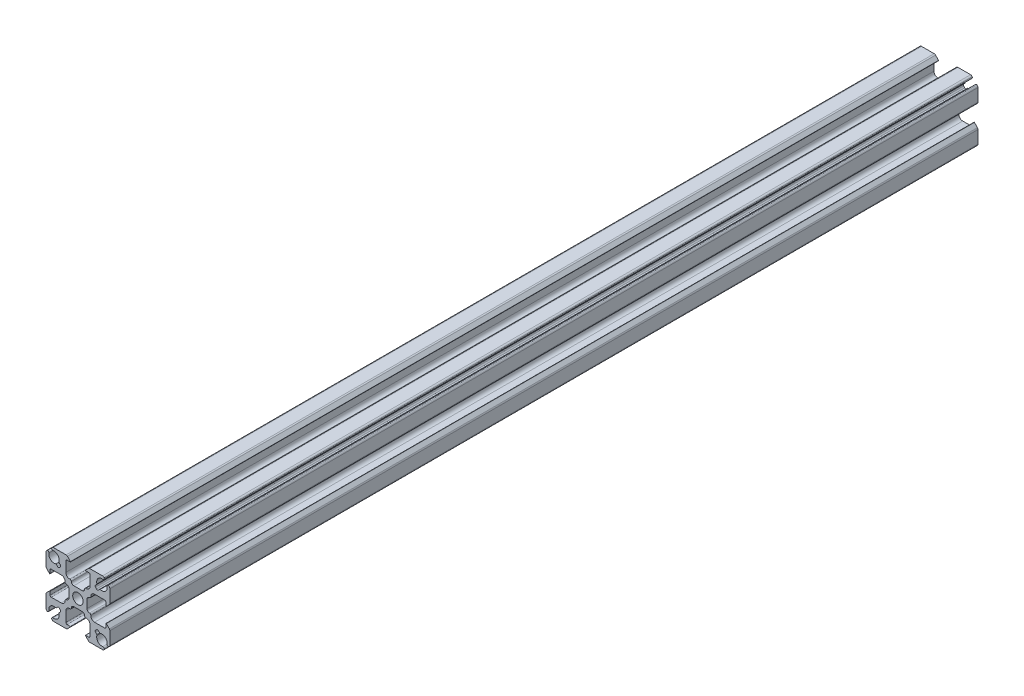
SolidWorks part; units mm, degrees
ref_plane "Front Plane" through (0, 0, 0) normal (0, 0, 1) x (1, 0, 0)
ref_plane "Top Plane" through (0, 0, 0) normal (0, 1, 0) x (1, 0, 0)
ref_plane "Right Plane" through (0, 0, 0) normal (1, 0, 0) x (0, 0, -1)
ref_plane "Plane1" through (0, 0, 0) normal (0, 0, -1) x (-1, 0, 0)
sketch "Sketch1" plane through (0, 0, 0) normal (0, 0, -1) x (-1, 0, 0)
  line L0 (-7.4885, 8.6199) -> (-6.9856, 8.117)
  line L1 (-6.9856, 7.4099) -> (-7.4099, 6.9856)
  line L2 (-8.117, 6.9856) -> (-8.6199, 7.4885)
  line L3 (-12.7, 9.7594) -> (-12.7, 4.7107)
  line L4 (-12.4803, 4.1803) -> (-11.2707, 2.9707)
  line L5 (-11.1, 3.0414) -> (-11.1, 4.325)
  line L6 (-10.6, 4.825) -> (-6.6, 4.825)
  line L7 (-5.1, 3.325) -> (-5.1, 3.15)
  line L8 (-3.6, 1.65) -> (-3.6, -1.65)
  line L9 (-5.1, -3.15) -> (-5.1, -3.325)
  line L10 (-6.6, -4.825) -> (-10.6, -4.825)
  line L11 (-11.1, -4.325) -> (-11.1, -3.0414)
  line L12 (-11.2707, -2.9707) -> (-12.4803, -4.1803)
  line L13 (-12.7, -4.7107) -> (-12.7, -9.7594)
  line L14 (-8.6199, -7.4885) -> (-8.117, -6.9856)
  line L15 (-7.4099, -6.9856) -> (-6.9856, -7.4099)
  line L16 (-6.9856, -8.117) -> (-7.4885, -8.6199)
  line L17 (-9.7594, -12.7) -> (-4.7107, -12.7)
  line L18 (-4.1803, -12.4803) -> (-2.9707, -11.2707)
  line L19 (-3.0414, -11.1) -> (-4.325, -11.1)
  line L20 (-4.825, -10.6) -> (-4.825, -6.6)
  line L21 (-3.325, -5.1) -> (-3.15, -5.1)
  line L22 (-1.65, -3.6) -> (1.65, -3.6)
  line L23 (3.15, -5.1) -> (3.325, -5.1)
  line L24 (4.825, -6.6) -> (4.825, -10.6)
  line L25 (4.325, -11.1) -> (3.0414, -11.1)
  line L26 (2.9707, -11.2707) -> (4.1803, -12.4803)
  line L27 (4.7107, -12.7) -> (9.7594, -12.7)
  line L28 (7.4885, -8.6199) -> (6.9856, -8.117)
  line L29 (6.9856, -7.4099) -> (7.4099, -6.9856)
  line L30 (8.117, -6.9856) -> (8.6199, -7.4885)
  line L31 (12.7, -9.7594) -> (12.7, -4.7107)
  line L32 (12.4803, -4.1803) -> (11.2707, -2.9707)
  line L33 (11.1, -3.0414) -> (11.1, -4.325)
  line L34 (10.6, -4.825) -> (6.6, -4.825)
  line L35 (5.1, -3.325) -> (5.1, -3.15)
  line L36 (3.6, -1.65) -> (3.6, 1.65)
  line L37 (5.1, 3.15) -> (5.1, 3.325)
  line L38 (6.6, 4.825) -> (10.6, 4.825)
  line L39 (11.1, 4.325) -> (11.1, 3.0414)
  line L40 (11.2707, 2.9707) -> (12.4803, 4.1803)
  line L41 (12.7, 4.7107) -> (12.7, 9.7594)
  line L42 (8.6199, 7.4885) -> (8.117, 6.9856)
  line L43 (7.4099, 6.9856) -> (6.9856, 7.4099)
  line L44 (6.9856, 8.117) -> (7.4885, 8.6199)
  line L45 (9.7594, 12.7) -> (4.7107, 12.7)
  line L46 (4.1803, 12.4803) -> (2.9707, 11.2707)
  line L47 (3.0414, 11.1) -> (4.325, 11.1)
  line L48 (4.825, 10.6) -> (4.825, 6.6)
  line L49 (3.325, 5.1) -> (3.15, 5.1)
  line L50 (1.65, 3.6) -> (-1.65, 3.6)
  line L51 (-3.15, 5.1) -> (-3.325, 5.1)
  line L52 (-4.825, 6.6) -> (-4.825, 10.6)
  line L53 (-4.325, 11.1) -> (-3.0414, 11.1)
  line L54 (-2.9707, 11.2707) -> (-4.1803, 12.4803)
  line L55 (-4.7107, 12.7) -> (-9.7594, 12.7)
  circle A0 centre (0, 0) radius 2.08
  arc A1 (-9.7594, 12.7) -> (-10.4266, 12.2927) centre (-9.7594, 11.95) ccw
  arc A2 (-10.4266, 12.2927) -> (-9.8933, 11.5721) centre (-9.9818, 12.0642) ccw
  arc A3 (-9.8933, 11.5721) -> (-7.5492, 8.8748) centre (-9.525, 9.525) cw
  arc A4 (-7.5492, 8.8748) -> (-7.4885, 8.6199) centre (-7.3118, 8.7967) ccw
  arc A5 (-6.9856, 8.117) -> (-6.9856, 7.4099) centre (-7.3392, 7.7635) cw
  arc A6 (-7.4099, 6.9856) -> (-8.117, 6.9856) centre (-7.7635, 7.3392) cw
  arc A7 (-8.6199, 7.4885) -> (-8.8748, 7.5492) centre (-8.7967, 7.3118) ccw
  arc A8 (-8.8748, 7.5492) -> (-11.5721, 9.8933) centre (-9.525, 9.525) cw
  arc A9 (-11.5721, 9.8933) -> (-12.2927, 10.4266) centre (-12.0642, 9.9818) ccw
  arc A10 (-12.2927, 10.4266) -> (-12.7, 9.7594) centre (-11.95, 9.7594) ccw
  arc A11 (-12.7, 4.7107) -> (-12.4803, 4.1803) centre (-11.95, 4.7107) ccw
  arc A12 (-11.2707, 2.9707) -> (-11.1, 3.0414) centre (-11.2, 3.0414) ccw
  arc A13 (-11.1, 4.325) -> (-10.6, 4.825) centre (-10.6, 4.325) cw
  arc A14 (-6.6, 4.825) -> (-5.1, 3.325) centre (-6.6, 3.325) cw
  arc A15 (-5.1, 3.15) -> (-4.6, 2.65) centre (-4.6, 3.15) ccw
  arc A16 (-4.6, 2.65) -> (-3.6, 1.65) centre (-4.6, 1.65) cw
  arc A17 (-3.6, -1.65) -> (-4.6, -2.65) centre (-4.6, -1.65) cw
  arc A18 (-4.6, -2.65) -> (-5.1, -3.15) centre (-4.6, -3.15) ccw
  arc A19 (-5.1, -3.325) -> (-6.6, -4.825) centre (-6.6, -3.325) cw
  arc A20 (-10.6, -4.825) -> (-11.1, -4.325) centre (-10.6, -4.325) cw
  arc A21 (-11.1, -3.0414) -> (-11.2707, -2.9707) centre (-11.2, -3.0414) ccw
  arc A22 (-12.4803, -4.1803) -> (-12.7, -4.7107) centre (-11.95, -4.7107) ccw
  arc A23 (-12.7, -9.7594) -> (-12.2927, -10.4266) centre (-11.95, -9.7594) ccw
  arc A24 (-12.2927, -10.4266) -> (-11.5721, -9.8933) centre (-12.0642, -9.9818) ccw
  arc A25 (-11.5721, -9.8933) -> (-8.8748, -7.5492) centre (-9.525, -9.525) cw
  arc A26 (-8.8748, -7.5492) -> (-8.6199, -7.4885) centre (-8.7967, -7.3118) ccw
  arc A27 (-8.117, -6.9856) -> (-7.4099, -6.9856) centre (-7.7635, -7.3392) cw
  arc A28 (-6.9856, -7.4099) -> (-6.9856, -8.117) centre (-7.3392, -7.7635) cw
  arc A29 (-7.4885, -8.6199) -> (-7.5492, -8.8748) centre (-7.3118, -8.7967) ccw
  arc A30 (-7.5492, -8.8748) -> (-9.8933, -11.5721) centre (-9.525, -9.525) cw
  arc A31 (-9.8933, -11.5721) -> (-10.4266, -12.2927) centre (-9.9818, -12.0642) ccw
  arc A32 (-10.4266, -12.2927) -> (-9.7594, -12.7) centre (-9.7594, -11.95) ccw
  arc A33 (-4.7107, -12.7) -> (-4.1803, -12.4803) centre (-4.7107, -11.95) ccw
  arc A34 (-2.9707, -11.2707) -> (-3.0414, -11.1) centre (-3.0414, -11.2) ccw
  arc A35 (-4.325, -11.1) -> (-4.825, -10.6) centre (-4.325, -10.6) cw
  arc A36 (-4.825, -6.6) -> (-3.325, -5.1) centre (-3.325, -6.6) cw
  arc A37 (-3.15, -5.1) -> (-2.65, -4.6) centre (-3.15, -4.6) ccw
  arc A38 (-2.65, -4.6) -> (-1.65, -3.6) centre (-1.65, -4.6) cw
  arc A39 (1.65, -3.6) -> (2.65, -4.6) centre (1.65, -4.6) cw
  arc A40 (2.65, -4.6) -> (3.15, -5.1) centre (3.15, -4.6) ccw
  arc A41 (3.325, -5.1) -> (4.825, -6.6) centre (3.325, -6.6) cw
  arc A42 (4.825, -10.6) -> (4.325, -11.1) centre (4.325, -10.6) cw
  arc A43 (3.0414, -11.1) -> (2.9707, -11.2707) centre (3.0414, -11.2) ccw
  arc A44 (4.1803, -12.4803) -> (4.7107, -12.7) centre (4.7107, -11.95) ccw
  arc A45 (9.7594, -12.7) -> (10.4266, -12.2927) centre (9.7594, -11.95) ccw
  arc A46 (10.4266, -12.2927) -> (9.8933, -11.5721) centre (9.9818, -12.0642) ccw
  arc A47 (9.8933, -11.5721) -> (7.5492, -8.8748) centre (9.525, -9.525) cw
  arc A48 (7.5492, -8.8748) -> (7.4885, -8.6199) centre (7.3118, -8.7967) ccw
  arc A49 (6.9856, -8.117) -> (6.9856, -7.4099) centre (7.3392, -7.7635) cw
  arc A50 (7.4099, -6.9856) -> (8.117, -6.9856) centre (7.7635, -7.3392) cw
  arc A51 (8.6199, -7.4885) -> (8.8748, -7.5492) centre (8.7967, -7.3118) ccw
  arc A52 (8.8748, -7.5492) -> (11.5721, -9.8933) centre (9.525, -9.525) cw
  arc A53 (11.5721, -9.8933) -> (12.2927, -10.4266) centre (12.0642, -9.9818) ccw
  arc A54 (12.2927, -10.4266) -> (12.7, -9.7594) centre (11.95, -9.7594) ccw
  arc A55 (12.7, -4.7107) -> (12.4803, -4.1803) centre (11.95, -4.7107) ccw
  arc A56 (11.2707, -2.9707) -> (11.1, -3.0414) centre (11.2, -3.0414) ccw
  arc A57 (11.1, -4.325) -> (10.6, -4.825) centre (10.6, -4.325) cw
  arc A58 (6.6, -4.825) -> (5.1, -3.325) centre (6.6, -3.325) cw
  arc A59 (5.1, -3.15) -> (4.6, -2.65) centre (4.6, -3.15) ccw
  arc A60 (4.6, -2.65) -> (3.6, -1.65) centre (4.6, -1.65) cw
  arc A61 (3.6, 1.65) -> (4.6, 2.65) centre (4.6, 1.65) cw
  arc A62 (4.6, 2.65) -> (5.1, 3.15) centre (4.6, 3.15) ccw
  arc A63 (5.1, 3.325) -> (6.6, 4.825) centre (6.6, 3.325) cw
  arc A64 (10.6, 4.825) -> (11.1, 4.325) centre (10.6, 4.325) cw
  arc A65 (11.1, 3.0414) -> (11.2707, 2.9707) centre (11.2, 3.0414) ccw
  arc A66 (12.4803, 4.1803) -> (12.7, 4.7107) centre (11.95, 4.7107) ccw
  arc A67 (12.7, 9.7594) -> (12.2927, 10.4266) centre (11.95, 9.7594) ccw
  arc A68 (12.2927, 10.4266) -> (11.5721, 9.8933) centre (12.0642, 9.9818) ccw
  arc A69 (11.5721, 9.8933) -> (8.8748, 7.5492) centre (9.525, 9.525) cw
  arc A70 (8.8748, 7.5492) -> (8.6199, 7.4885) centre (8.7967, 7.3118) ccw
  arc A71 (8.117, 6.9856) -> (7.4099, 6.9856) centre (7.7635, 7.3392) cw
  arc A72 (6.9856, 7.4099) -> (6.9856, 8.117) centre (7.3392, 7.7635) cw
  arc A73 (7.4885, 8.6199) -> (7.5492, 8.8748) centre (7.3118, 8.7967) ccw
  arc A74 (7.5492, 8.8748) -> (9.8933, 11.5721) centre (9.525, 9.525) cw
  arc A75 (9.8933, 11.5721) -> (10.4266, 12.2927) centre (9.9818, 12.0642) ccw
  arc A76 (10.4266, 12.2927) -> (9.7594, 12.7) centre (9.7594, 11.95) ccw
  arc A77 (4.7107, 12.7) -> (4.1803, 12.4803) centre (4.7107, 11.95) ccw
  arc A78 (2.9707, 11.2707) -> (3.0414, 11.1) centre (3.0414, 11.2) ccw
  arc A79 (4.325, 11.1) -> (4.825, 10.6) centre (4.325, 10.6) cw
  arc A80 (4.825, 6.6) -> (3.325, 5.1) centre (3.325, 6.6) cw
  arc A81 (3.15, 5.1) -> (2.65, 4.6) centre (3.15, 4.6) ccw
  arc A82 (2.65, 4.6) -> (1.65, 3.6) centre (1.65, 4.6) cw
  arc A83 (-1.65, 3.6) -> (-2.65, 4.6) centre (-1.65, 4.6) cw
  arc A84 (-2.65, 4.6) -> (-3.15, 5.1) centre (-3.15, 4.6) ccw
  arc A85 (-3.325, 5.1) -> (-4.825, 6.6) centre (-3.325, 6.6) cw
  arc A86 (-4.825, 10.6) -> (-4.325, 11.1) centre (-4.325, 10.6) cw
  arc A87 (-3.0414, 11.1) -> (-2.9707, 11.2707) centre (-3.0414, 11.2) ccw
  arc A88 (-4.1803, 12.4803) -> (-4.7107, 12.7) centre (-4.7107, 11.95) ccw
extrude "Boss-Extrude1" add sketch "Sketch1" against normal mid plane 345.1098
hole_wizard "Tap Drill for M6x1.0 Tap2" positions "Sketch3" profile "Sketch2" hole size "M6x1.0" standard "ANSI Metric"
sketch "Sketch3" plane through (3.6, 0, 0) normal (1, 0, 0) x (0, 0, -1)
  point P0 (-120.8849, -4.45)
  point P3 (15.0051, -4.45)
  point P6 (-120.8849, -4.45)
sketch "Sketch2" plane through (3.6, -4.45, 120.8849) normal (0, 1, 0) x (0, 0, -1)
  line L0 (0, 0) -> (0, 16.3)
  line L1 (0, 16.3) -> (2.5, 16.3)
  line L2 (2.5, 16.3) -> (2.5, 0)
  line L5 (2.5, 0) -> (0, 0)
  line L11 (0, -6.35) -> (0, 107.95) construction
  dimension "Thru Hole Dia." = 5
  dimension "Thru Hole Depth" = 16.3
hole_wizard "Tap Drill for M6x1.0 Tap1" positions "Sketch5" profile "Sketch4" hole size "M6x1.0" standard "ANSI Metric"
sketch "Sketch5" plane through (-3.6, 0, 0) normal (-1, 0, 0) x (0, 0, 1)
  point P0 (151.6049, 0)
  point P3 (31.6049, 0)
  point P6 (-88.3951, 0)
sketch "Sketch4" plane through (-3.6, 0, 151.6049) normal (0, 1, 0) x (0, 0, 1)
  line L0 (0, 0) -> (0, 16.3)
  line L1 (0, 16.3) -> (2.5, 16.3)
  line L2 (2.5, 16.3) -> (2.5, 0)
  line L5 (2.5, 0) -> (0, 0)
  line L11 (0, -6.35) -> (0, 107.95) construction
  dimension "Thru Hole Dia." = 5
  dimension "Thru Hole Depth" = 16.3
